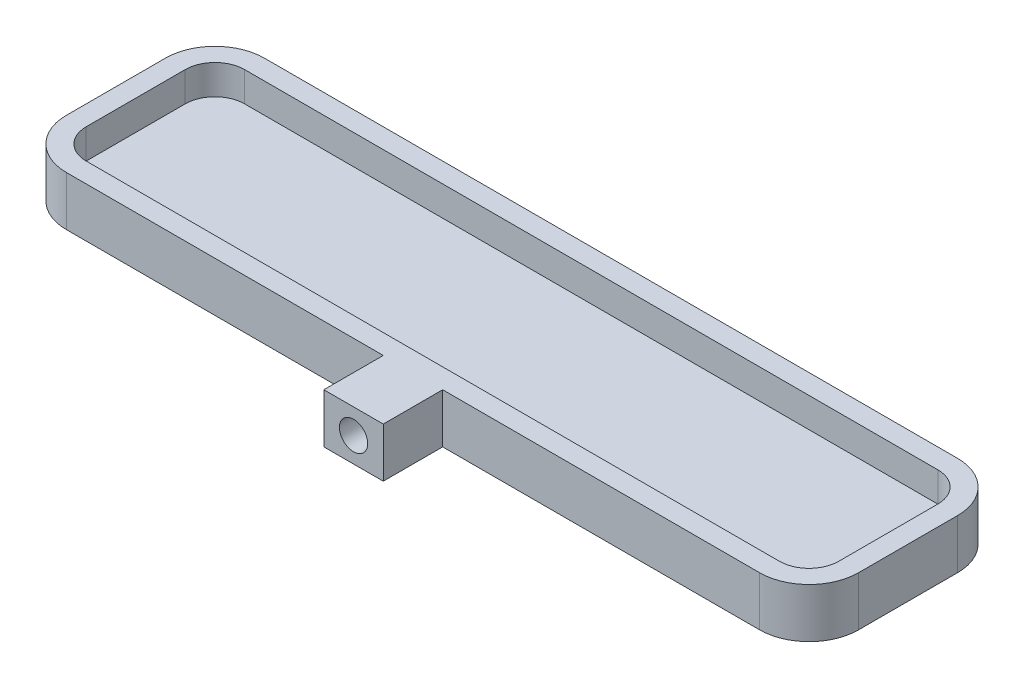
SolidWorks part; units mm, degrees
ref_plane "Front Plane" through (0, 0, 0) normal (0, 0, 1) x (1, 0, 0)
ref_plane "Top Plane" through (0, 0, 0) normal (0, 1, 0) x (1, 0, 0)
ref_plane "Right Plane" through (0, 0, 0) normal (1, 0, 0) x (0, 0, -1)
sketch "Sketch1" plane through (0, 0, 0) normal (0, 1, 0) x (1, 0, 0)
  line L1 (-40, 10) -> (40, 10)
  line L2 (-40, 10) -> (-40, -10)
  line L3 (-40, -10) -> (40, -10)
  line L4 (40, 10) -> (40, -10)
  line L5 (-40, 10) -> (40, -10) construction
  line L6 (-40, -10) -> (40, 10) construction
  point P0 (0, 0)
  dimension "D1" = 80
  dimension "D2" = 20
extrude "Boss-Extrude1" add sketch "Sketch1" along normal blind 5 contours L1 L4 L3 L2
fillet "Fillet1" radius 5 4 edges at (40, 2.5, -10) (40, 2.5, 10) (-40, 2.5, 10) (-40, 2.5, -10)
shell "Shell1" thickness 2
sketch "Sketch3" plane through (0, 0, 10) normal (0, 0, 1) x (1, 0, 0)
  line L0 (-35, 0) -> (35, 0) construction
  line L1 (-3, 5) -> (3, 5)
  line L2 (-3, 5) -> (-3, 0)
  line L3 (-3, 0) -> (3, 0)
  line L4 (3, 5) -> (3, 0)
  line L5 (-3, 5) -> (3, 0) construction
  line L6 (-3, 0) -> (3, 5) construction
  line L7 (-35, 5) -> (35, 5) construction
  line L8 (0, 8.0399) -> (0, -3.3201) construction
  point P0 (0, 2.5)
  dimension "D1" = 6
extrude "Boss-Extrude2" add sketch "Sketch3" along normal blind 6
sketch "Sketch5" plane through (0, 0, 16) normal (0, 0, 1) x (1, 0, 0)
  line L0 (0, 6.5884) -> (0, -1.537) construction
  line L1 (-5.1235, 2.5) -> (5.6642, 2.5) construction
  line L2 (3, 5) -> (-3, 5) construction
  line L3 (-3, 0) -> (3, 0) construction
  circle A0 centre (0, 2.5) radius 1.425
  dimension "D1" = 2.85
extrude "Cut-Extrude1" cut sketch "Sketch5" against normal blind 4
